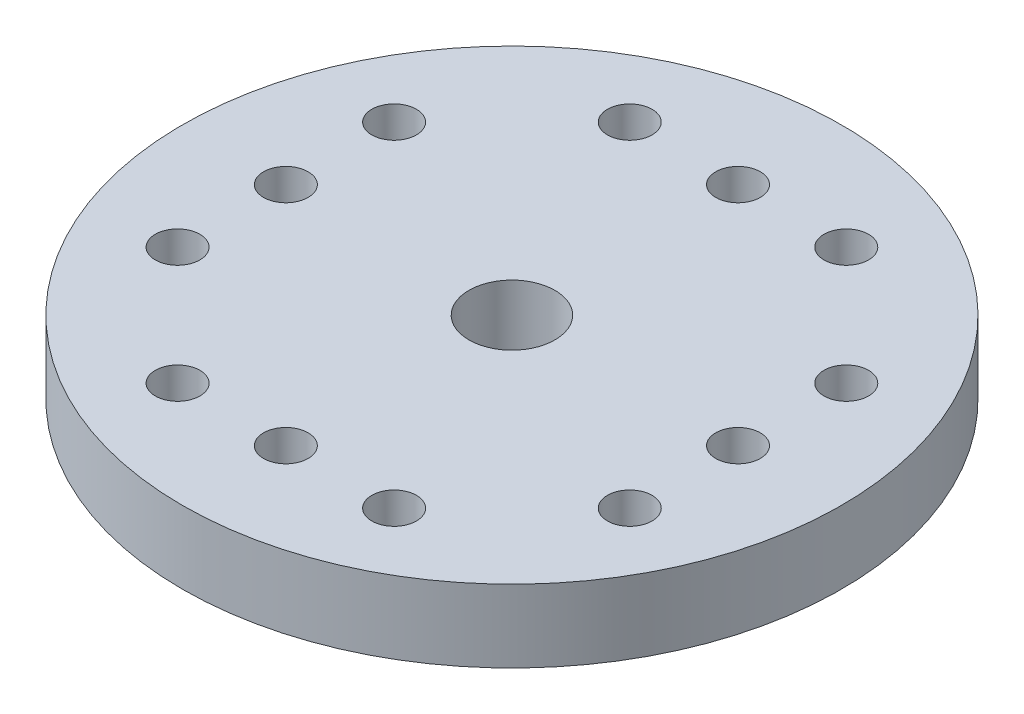
SolidWorks part; units mm, degrees
ref_plane "Front Plane" through (0, 0, 0) normal (0, 0, 1) x (1, 0, 0)
ref_plane "Top Plane" through (0, 0, 0) normal (0, 1, 0) x (1, 0, 0)
ref_plane "Right Plane" through (0, 0, 0) normal (1, 0, 0) x (0, 0, -1)
sketch "Sketch1" plane through (0, 0, 0) normal (0, 1, 0) x (1, 0, 0)
  circle A0 centre (0, 0) radius 10.35
  dimension "D1" = 20.7
extrude "Boss-Extrude1" add sketch "Sketch1" against normal blind 2.28
sketch "Sketch2" plane through (0, -2.28, 0) normal (0, -1, 0) x (1, 0, 0)
  circle A0 centre (0, 0) radius 4.35
  dimension "D1" = 8.7
extrude "Boss-Extrude2" add sketch "Sketch2" along normal blind 3.1
sketch "Sketch3" plane through (0, 0, 0) normal (0, 1, 0) x (1, 0, 0)
  circle A0 centre (0, 0) radius 1.35
  dimension "D1" = 2.7
extrude "Cut-Extrude1" cut sketch "Sketch3" against normal through all
sketch "Sketch4" plane through (0, -5.38, 0) normal (0, -1, 0) x (1, 0, 0)
  circle A0 centre (0, 0) radius 2.65
extrude "Cut-Extrude2" cut sketch "Sketch4" against normal up to surface (3.1 mm away) up to face at (0, -2.28, -4.35)
sketch "Sketch5" plane through (0, 0, 0) normal (0, 1, 0) x (1, 0, 0)
  line L0 (0, 0) -> (10.35, 0) construction
  line L1 (7.1, 3.4) -> (7.1, -3.4) construction
  circle A0 centre (0, 0) radius 10.35 construction
  circle A1 centre (7.1, 3.4) radius 0.7
  circle A2 centre (7.1, 0) radius 0.7
  circle A3 centre (7.1, -3.4) radius 0.7
  point P9 (7.1, 0)
  dimension "D1" = 1.4
  dimension "D2" = 6.8
  dimension "D3" = 3.25
extrude "Cut-Extrude3" cut sketch "Sketch5" against normal blind 3.1
pattern_circular "CirPattern1" count 4 over 360 about axis through (0, 0, 0) along (0, 1, 0) of "Cut-Extrude3"
